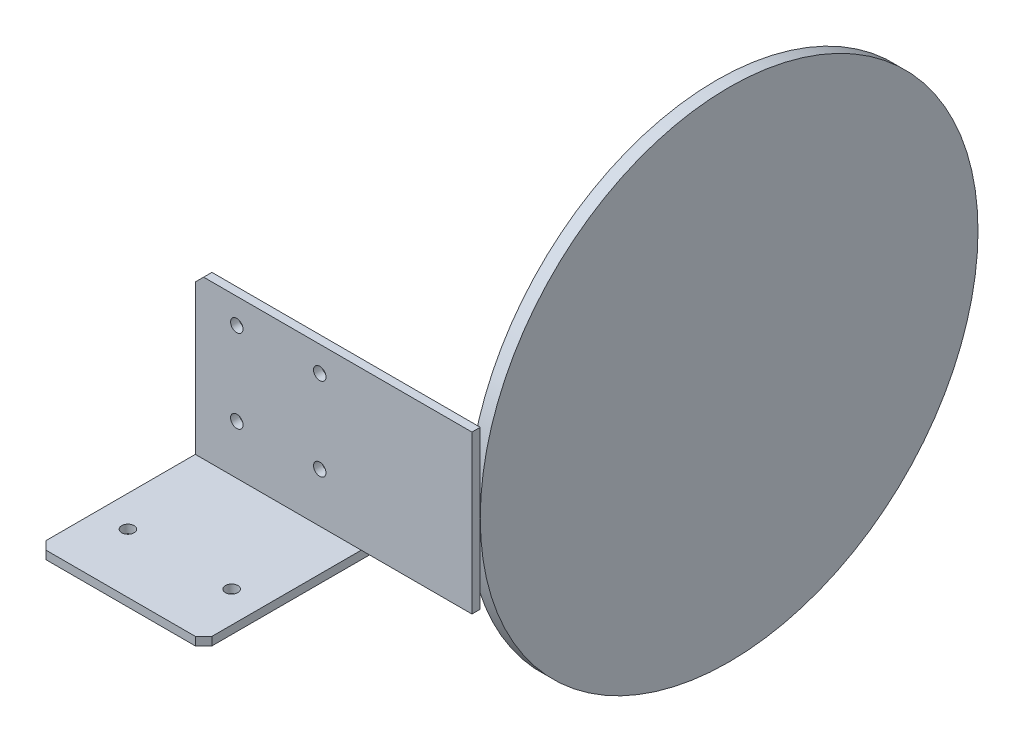
SolidWorks part; units mm, degrees
ref_plane "Спереди" through (0, 0, 0) normal (0, 0, 1) x (1, 0, 0)
ref_plane "Сверху" through (0, 0, 0) normal (0, 1, 0) x (1, 0, 0)
ref_plane "Справа" through (0, 0, 0) normal (1, 0, 0) x (0, 0, -1)
sketch "Sketch1" plane through (0, 0, 0) normal (1, 0, 0) x (0, 0, -1)
  line L0 (0, 0) -> (0, 38)
  line L1 (0, 38) -> (2, 38)
  line L2 (2, 38) -> (2, -2)
  line L3 (2, -2) -> (-38, -2)
  line L4 (-38, -2) -> (-38, 0)
  line L5 (-38, 0) -> (0, 0)
  dimension "D1" = 2
  dimension "D2" = 2
  dimension "D3" = 40
  dimension "D4" = 40
extrude "Extrude1" add sketch "Sketch1" along normal blind 40
sketch "Sketch2" plane through (0, -2, 0) normal (0, -1, 0) x (-1, 0, 0)
  line L0 (-40, 2) -> (0, 2) construction
  line L1 (-7.5, -23.75) -> (-32.5, -23.75) construction
  line L2 (-40, -38) -> (0, -38) construction
  circle A0 centre (-32.5, -23.75) radius 1.5
  circle A1 centre (-7.5, -23.75) radius 1.5
  point P5 (-20, -23.75)
  point P10 (-20, -38)
  dimension "D1" = 3
  dimension "D2" = 25
  dimension "D3" = 25.75
extrude "Extrude2" cut sketch "Sketch2" against normal up to next contours A0
sketch "Sketch3" plane through (0, 0, -2) normal (0, 0, -1) x (-1, 0, 0)
  line L1 (0, -2) -> (0, 38) construction
  line L2 (-40, 38) -> (0, 38) construction
  circle A0 centre (-10, 31.9) radius 1.5
  circle A1 centre (-30, 31.9) radius 1.5
  circle A2 centre (-30, 11.9) radius 1.5
  circle A3 centre (-10, 11.9) radius 1.5
  dimension "D1" = 10
  dimension "D2" = 6.1
  dimension "D3" = 2
  dimension "D4" = 2
extrude "Extrude3" cut sketch "Sketch3" against normal up to next
chamfer "Chamfer1" distance 2 angle 45 4 edges at (40, -1, 38) (0, -1, 38) (0, 38, -1) (40, 38, -1)
sketch "Sketch4" plane through (40, 0, 0) normal (1, 0, 0) x (0, 0, -1)
  line L0 (0, 36) -> (0, 38) construction
  line L1 (0, 38) -> (2, 38)
  line L2 (0, 38) -> (0, 0)
  line L3 (0, 0) -> (2, 0)
  line L4 (2, 38) -> (2, 0)
  line L5 (2, -2) -> (2, 36) construction
  line L6 (0, 38) -> (2, 38) construction
extrude "Boss-Extrude1" add sketch "Sketch4" along normal blind 26.69 and the other way blind 3
sketch "Sketch5" plane through (66.69, 0, 0) normal (1, 0, 0) x (0, 0, -1)
  line L2 (2, 0) -> (2, 38) construction
  circle A0 centre (62, 19) radius 60
  point P2 (2, 19)
  dimension "D1" = 120
extrude "Boss-Extrude2" add sketch "Sketch5" against normal blind 3 separate body contours A0
